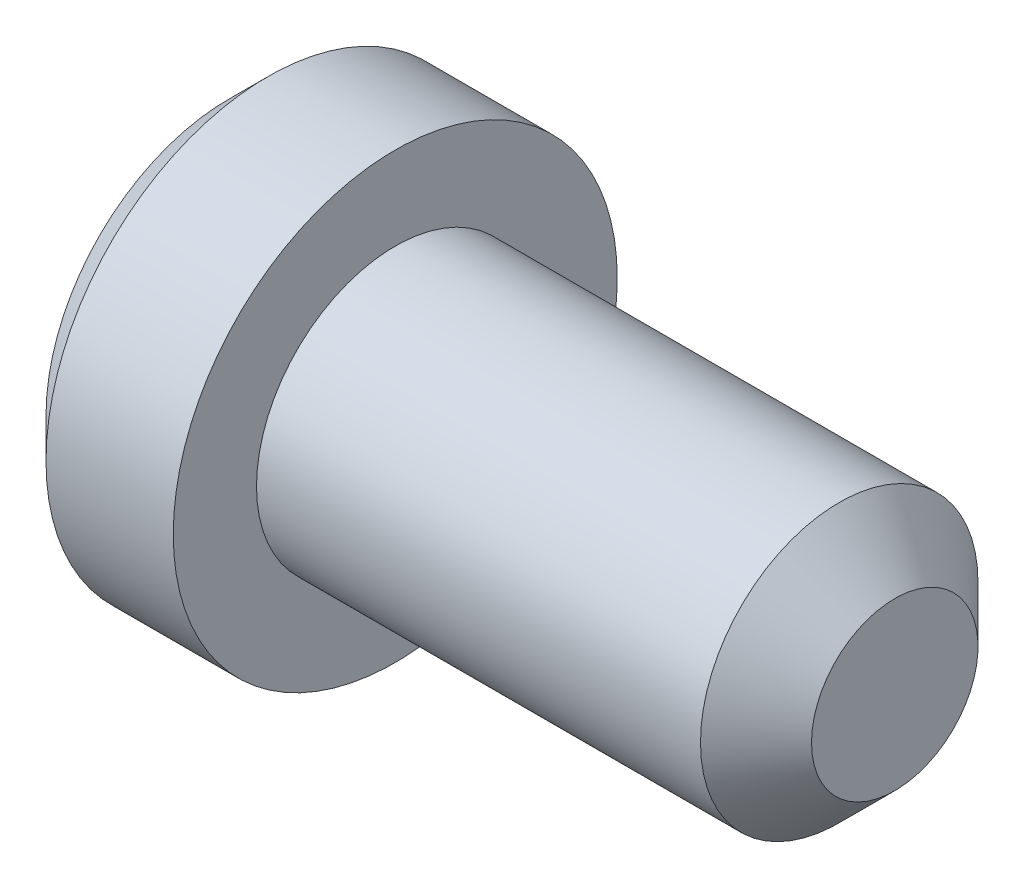
SolidWorks part; units mm, degrees
ref_plane "Front Plane" through (0, 0, 0) normal (0, 0, 1) x (1, 0, 0)
ref_plane "Top Plane" through (0, 0, 0) normal (0, 1, 0) x (1, 0, 0)
ref_plane "Right Plane" through (0, 0, 0) normal (1, 0, 0) x (0, 0, -1)
sketch "Sketch1" plane through (0, 0, 0) normal (0, 0, 1) x (1, 0, 0)
  line L0 (-137.6251, 0) -> (149.8618, 0) construction
  line L1 (0, 102.7059) -> (0, -81.5806) construction
  line L2 (-30, 0) -> (-30, -32.9289)
  line L3 (-30, -32.9289) -> (-22.9289, -40)
  line L4 (-22.9289, -40) -> (0, -40)
  line L5 (0, -40) -> (0, -25)
  line L6 (0, -25) -> (80, -25)
  line L7 (80, -25) -> (90, -15)
  line L8 (90, -15) -> (90, 0)
  line L9 (-30, 0) -> (90, 0)
  line L10 (-30, 23.1543) -> (-30, -124.4273) construction
  line L11 (90, 36.45) -> (90, -128.0837) construction
  dimension "D1" = 120
  dimension "D2" = 90
  dimension "D3" = 10
  dimension "D4" = 45
  dimension "D5" = 45
  dimension "D6" = 80
  dimension "D7" = 50
  dimension "D8" = 30
revolve "Revolve1" add sketch "Sketch1" angle 360 about L0
